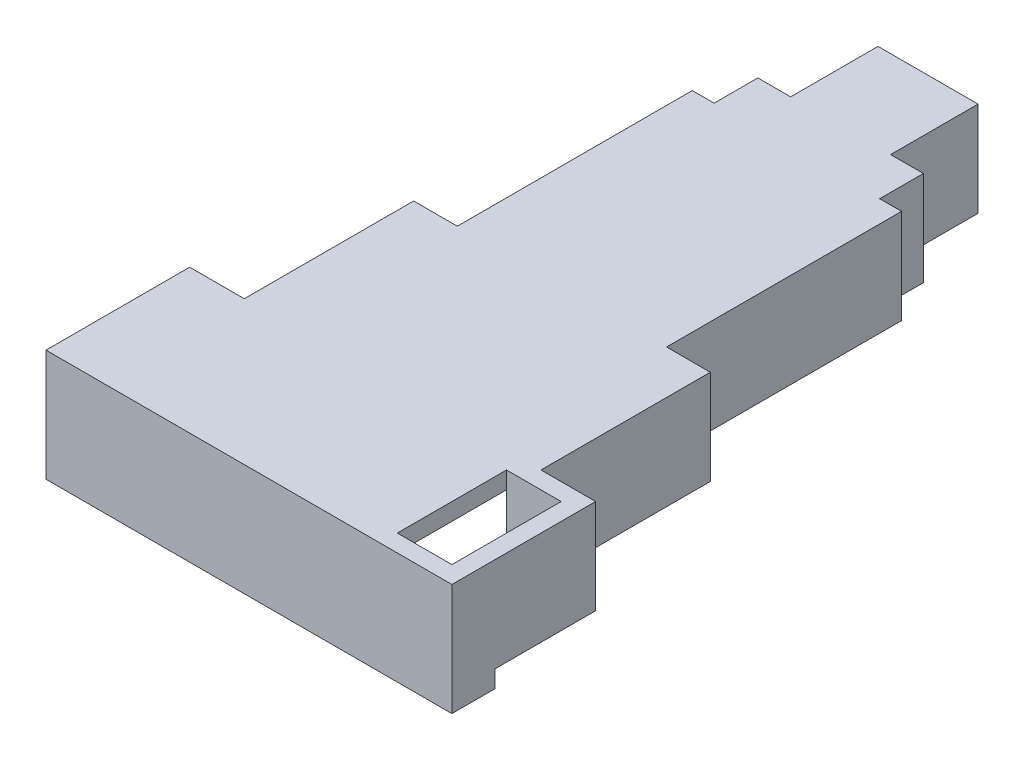
SolidWorks part; units mm, degrees
ref_plane "Front Plane" through (0, 0, 0) normal (0, 0, 1) x (1, 0, 0)
ref_plane "Top Plane" through (0, 0, 0) normal (0, 1, 0) x (1, 0, 0)
ref_plane "Right Plane" through (0, 0, 0) normal (1, 0, 0) x (0, 0, -1)
sketch "Sketch1" plane through (0, 0, 0) normal (0, 1, 0) x (1, 0, 0)
  line L0 (0, 0) -> (0, 12.7)
  line L1 (0, 12.7) -> (6.35, 12.7)
  line L2 (6.35, 12.7) -> (6.35, 32.38)
  line L3 (6.35, 32.38) -> (11.43, 32.38)
  line L4 (11.43, 32.38) -> (11.43, 59.69)
  line L5 (11.43, 59.69) -> (13.97, 59.69)
  line L6 (13.97, 59.69) -> (13.97, 64.77)
  line L7 (13.97, 64.77) -> (17.78, 64.77)
  line L8 (17.78, 64.77) -> (17.78, 74.93)
  line L9 (17.78, 74.93) -> (25.4, 74.93)
  line L10 (0, 0) -> (43.18, 0)
  line L11 (21.59, 74.93) -> (21.59, 0) construction
  line L12 (29.21, 59.69) -> (29.21, 64.77)
  line L13 (31.75, 59.69) -> (29.21, 59.69)
  line L14 (31.75, 32.38) -> (31.75, 59.69)
  line L15 (36.83, 32.38) -> (31.75, 32.38)
  line L16 (36.83, 12.7) -> (36.83, 32.38)
  line L17 (43.18, 12.7) -> (36.83, 12.7)
  line L18 (43.18, 0) -> (43.18, 12.7)
  line L19 (29.21, 64.77) -> (25.4, 64.77)
  line L20 (25.4, 64.77) -> (25.4, 74.93)
  line L21 (9.43, 34.38) -> (9.43, 61.69)
  line L22 (9.43, 61.69) -> (11.97, 61.69)
  line L23 (11.97, 61.69) -> (11.97, 66.77)
  line L24 (11.97, 66.77) -> (15.78, 66.77)
  line L25 (15.78, 66.77) -> (15.78, 76.93)
  line L26 (15.78, 76.93) -> (27.4, 76.93)
  line L27 (27.4, 66.77) -> (27.4, 76.93)
  line L28 (31.21, 66.77) -> (27.4, 66.77)
  line L29 (31.21, 61.69) -> (31.21, 66.77)
  line L30 (33.75, 61.69) -> (31.21, 61.69)
  line L31 (33.75, 34.38) -> (33.75, 61.69)
  line L32 (38.83, 34.38) -> (33.75, 34.38)
  line L33 (38.83, 14.7) -> (38.83, 34.38)
  line L34 (45.18, 14.7) -> (38.83, 14.7)
  line L35 (45.18, -2) -> (45.18, 14.7)
  line L36 (-2, -2) -> (45.18, -2)
  line L37 (-2, -2) -> (-2, 14.7)
  line L38 (-2, 14.7) -> (4.35, 14.7)
  line L39 (4.35, 14.7) -> (4.35, 34.38)
  line L40 (4.35, 34.38) -> (9.43, 34.38)
  dimension "D1" = 12.7
  dimension "D2" = 6.35
  dimension "D3" = 19.68
  dimension "D4" = 5.08
  dimension "D5" = 27.31
  dimension "D6" = 2.54
  dimension "D7" = 5.08
  dimension "D8" = 3.81
  dimension "D9" = 10.16
  dimension "D10" = 2
  dimension "D11" = 21.59
extrude "Boss-Extrude2" add sketch "Sketch1" along normal blind 9
sketch "Sketch2" plane through (0, 9, 0) normal (0, 1, 0) x (1, 0, 0)
  line L0 (-2, -2) -> (-2, 14.7)
  line L1 (-2, 14.7) -> (4.35, 14.7)
  line L2 (4.35, 14.7) -> (4.35, 34.38)
  line L3 (4.35, 34.38) -> (4.35, 14.7) construction
  line L4 (4.35, 34.38) -> (9.43, 34.38)
  line L5 (9.43, 34.38) -> (9.43, 61.69)
  line L6 (9.43, 61.69) -> (11.97, 61.69)
  line L7 (11.97, 61.69) -> (11.97, 66.77)
  line L8 (11.97, 66.77) -> (15.78, 66.77)
  line L9 (15.78, 66.77) -> (15.78, 76.93)
  line L10 (15.78, 76.93) -> (27.4, 76.93)
  line L11 (27.4, 76.93) -> (27.4, 66.77)
  line L12 (27.4, 66.77) -> (31.21, 66.77)
  line L13 (31.21, 66.77) -> (31.21, 61.69)
  line L14 (31.21, 61.69) -> (33.75, 61.69)
  line L15 (33.75, 61.69) -> (33.75, 34.38)
  line L16 (33.75, 34.38) -> (38.83, 34.38)
  line L17 (38.83, 34.38) -> (38.83, 14.7)
  line L18 (38.83, 14.7) -> (45.18, 14.7)
  line L19 (45.18, 14.7) -> (45.18, -2)
  line L20 (45.18, -2) -> (-2, -2)
extrude "Boss-Extrude3" add sketch "Sketch2" along normal blind 2
sketch "Sketch3" plane through (0, 0, 0) normal (0, -1, 0) x (1, 0, 0)
  line L0 (45.18, 2) -> (45.18, -14.7) construction
  line L1 (-2, 2) -> (45.18, 2)
  line L2 (-2, 2) -> (-2, -3)
  line L3 (-2, -3) -> (45.18, -3)
  line L4 (45.18, 2) -> (45.18, -3)
  dimension "D1" = 5
extrude "Boss-Extrude4" add sketch "Sketch3" along normal blind 2
sketch "Sketch5" plane through (0, 9, 0) normal (0, -1, 0) x (1, 0, 0)
  line L1 (43.18, -12.7) -> (36.83, -12.7)
  line L2 (43.18, -12.7) -> (43.18, 0)
  line L3 (43.18, 0) -> (36.83, 0)
  line L4 (36.83, -12.7) -> (36.83, 0)
extrude "Cut-Extrude1" cut sketch "Sketch5" against normal blind 10 and the other way through all
sketch "Sketch8" plane through (0, 0, -59.69) normal (0, 0, 1) x (1, 0, 0)
  line L0 (11.43, 0) -> (12.43, 1)
  line L2 (11.43, 9) -> (11.43, 0) construction
  line L3 (11.43, 1) -> (11.43, 0)
  line L4 (12.43, 1) -> (11.43, 2)
  line L5 (11.43, 2) -> (11.43, 1)
  dimension "D1" = 1
  dimension "D2" = 1
  dimension "D3" = 1
extrude "Boss-Extrude5" add sketch "Sketch8" along normal blind 10 from offset 8
sketch "Sketch9" plane through (0, 0, -59.69) normal (0, 0, 1) x (1, 0, 0)
  line L0 (31.75, 0) -> (31.75, 1)
  line L1 (31.75, 9) -> (31.75, 0) construction
  line L3 (30.75, 1) -> (31.75, 0)
  line L4 (30.75, 1) -> (31.75, 2)
  line L5 (31.75, 2) -> (31.75, 1)
  dimension "D1" = 1
  dimension "D2" = 1
  dimension "D3" = 1
extrude "Boss-Extrude6" add sketch "Sketch9" along normal blind 10 from offset 8
sketch "Sketch10" plane through (0, -2, 0) normal (0, -1, 0) x (1, 0, 0)
  line L0 (-2, -3) -> (36.83, -3) construction
  line L1 (31.2702, -3) -> (10.5822, -3)
  line L3 (31.2702, 0) -> (10.5822, 0)
  line L4 (10.5822, -3) -> (10.5822, 0)
  line L6 (42.3898, -6) -> (31.2702, -6)
  line L7 (42.3898, -6) -> (42.3898, 0)
  line L8 (42.3898, 0) -> (31.2702, 0)
  line L9 (31.2702, -6) -> (31.2702, -3)
  line L10 (42.3898, -6) -> (31.2702, 0) construction
  line L11 (42.3898, 0) -> (31.2702, -6) construction
  point P6 (36.83, -3)
extrude "Cut-Extrude2" cut sketch "Sketch10" against normal blind 8
